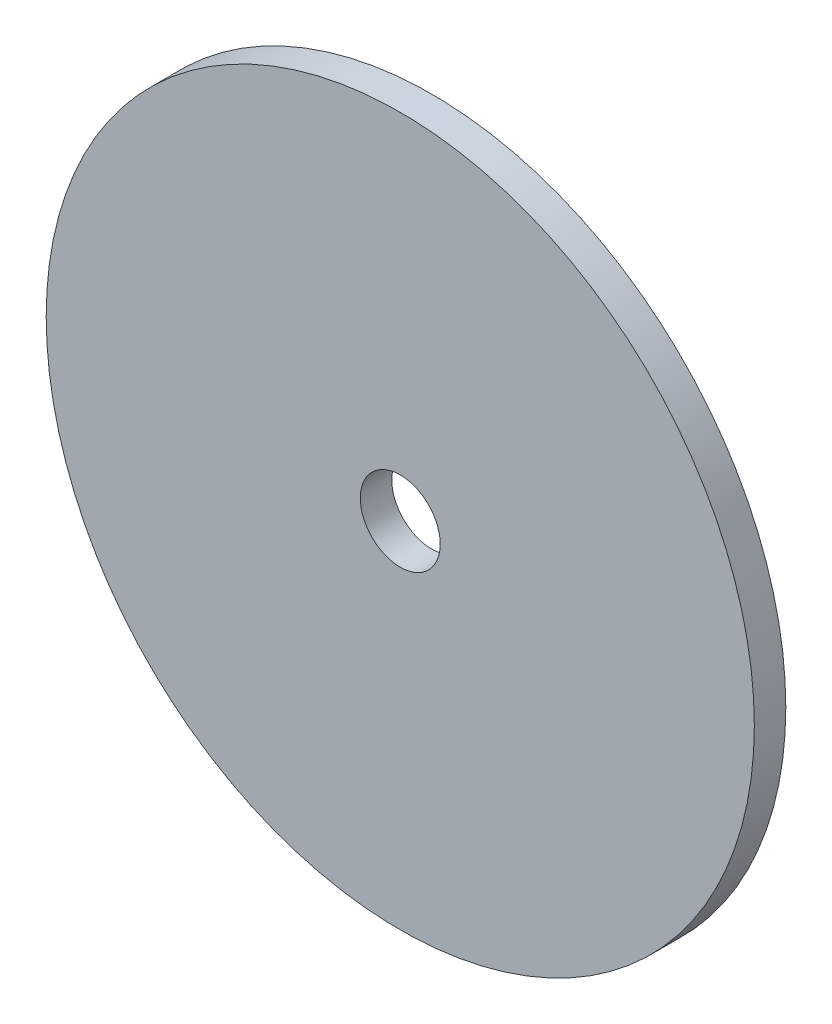
SolidWorks part; units mm, degrees
ref_plane "Front Plane" through (0, 0, 0) normal (0, 0, 1) x (1, 0, 0)
ref_plane "Top Plane" through (0, 0, 0) normal (0, 1, 0) x (1, 0, 0)
ref_plane "Right Plane" through (0, 0, 0) normal (1, 0, 0) x (0, 0, -1)
sketch "Sketch1" plane through (0, 0, 0) normal (0, 0, 1) x (1, 0, 0)
  circle A0 centre (0, 0) radius 225
  circle A1 centre (0, 0) radius 25.4
  dimension "D1" = 450
  dimension "D2" = 50.8
extrude "Boss-Extrude1" add sketch "Sketch1" along normal blind 20
